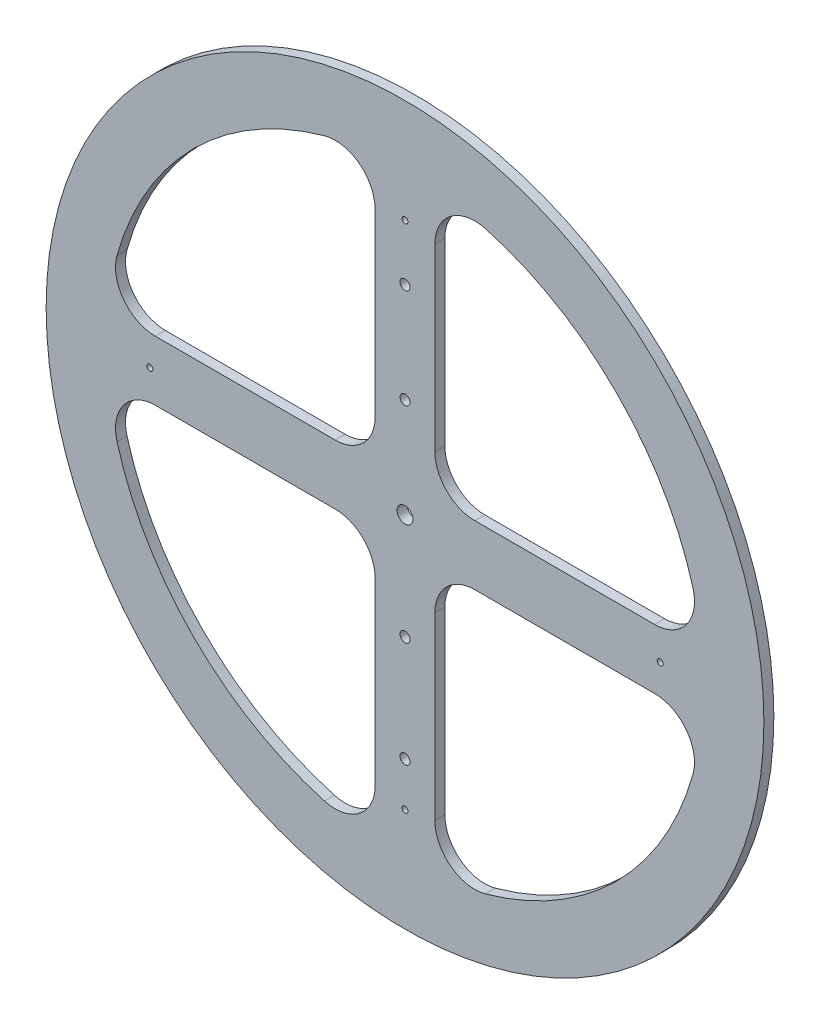
SolidWorks part; units mm, degrees
other "DetailItem2"
ref_plane "Front Plane" through (0, 0, 0) normal (0, 0, 1) x (1, 0, 0)
ref_plane "Top Plane" through (0, 0, 0) normal (0, 1, 0) x (1, 0, 0)
ref_plane "Right Plane" through (0, 0, 0) normal (1, 0, 0) x (0, 0, -1)
sketch "Sketch1" plane through (0, 0, 0) normal (0, 0, 1) x (1, 0, 0)
  line L0 (-150, 0) -> (150, 0) construction
  line L1 (0, 150) -> (0, -150) construction
  line L2 (-15, 125.1998) -> (-15, 35)
  line L3 (15, 125.1998) -> (15, 35)
  line L4 (-15, 150) -> (-15, -150) construction
  line L5 (0, 0) -> (228.291, 228.291) construction
  line L6 (125.1998, 15) -> (35, 15)
  line L7 (125.1998, -15) -> (35, -15)
  line L8 (15, -35) -> (15, -125.1998)
  line L9 (-15, -35) -> (-15, -125.1998)
  line L10 (-35, -15) -> (-125.1998, -15)
  line L11 (-35, 15) -> (-125.1998, 15)
  circle A0 centre (0, 0) radius 180
  arc A1 (144.4614, 40.3846) -> (40.3846, 144.4614) centre (0, 0) ccw
  arc A2 (-40.3846, 144.4614) -> (-144.4614, 40.3846) centre (0, 0) ccw
  arc A3 (40.3846, -144.4614) -> (144.4614, -40.3846) centre (0, 0) ccw
  arc A4 (-144.4614, -40.3846) -> (-40.3846, -144.4614) centre (0, 0) ccw
  arc A5 (-125.1998, -15) -> (-144.4614, -40.3846) centre (-125.1998, -35) ccw
  arc A6 (-15, -125.1998) -> (-40.3846, -144.4614) centre (-35, -125.1998) cw
  arc A7 (40.3846, -144.4614) -> (15, -125.1998) centre (35, -125.1998) cw
  arc A8 (144.4614, -40.3846) -> (125.1998, -15) centre (125.1998, -35) ccw
  arc A9 (125.1998, 15) -> (144.4614, 40.3846) centre (125.1998, 35) ccw
  arc A10 (40.3846, 144.4614) -> (15, 125.1998) centre (35, 125.1998) ccw
  arc A11 (-15, 125.1998) -> (-40.3846, 144.4614) centre (-35, 125.1998) ccw
  arc A12 (-144.4614, 40.3846) -> (-125.1998, 15) centre (-125.1998, 35) ccw
  arc A13 (-35, -15) -> (-15, -35) centre (-35, -35) cw
  arc A14 (15, -35) -> (35, -15) centre (35, -35) cw
  arc A15 (35, 15) -> (15, 35) centre (35, 35) cw
  arc A16 (-15, 35) -> (-35, 15) centre (-35, 35) cw
  point P24 (-149.2481, -15)
  point P27 (-15, -149.2481)
  point P30 (15, -149.2481)
  point P33 (149.2481, -15)
  point P36 (149.2481, 15)
  point P39 (15, 149.2481)
  point P42 (-15, 149.2481)
  point P45 (-149.2481, 15)
  point P48 (-15, -15)
  point P53 (15, 15)
  dimension "D1" = 360
  dimension "D2" = 300
  dimension "D5" = 20
  dimension "D4" = 45
  dimension "D3" = 15
extrude "Boss-Extrude1" add sketch "Sketch1" along normal blind 5
sketch "Sketch2" plane through (0, 0, 5) normal (0, 0, 1) x (1, 0, 0)
  circle A0 centre (0, 0) radius 4
  dimension "D1" = 8
extrude "Cut-Extrude1" cut sketch "Sketch2" against normal through all
sketch "Sketch3" plane through (0, 0, 5) normal (0, 0, 1) x (1, 0, 0)
  line L0 (0, 0) -> (0, 149.8543) construction
  line L1 (0, 0) -> (0, -168.5485) construction
  circle A0 centre (0, 50) radius 2.5
  circle A1 centre (0, 100) radius 2.5
  circle A2 centre (0, -53) radius 2.5
  circle A3 centre (0, -106) radius 2.5
  circle A4 centre (0, 0) radius 4 construction
  dimension "D1" = 5
  dimension "D3" = 50
  dimension "D4" = 53
  dimension "D5" = 53
  dimension "D2" = 50
extrude "Cut-Extrude2" cut sketch "Sketch3" against normal through all
sketch "Sketch4" plane through (0, 0, 5) normal (0, 0, 1) x (1, 0, 0)
  circle A0 centre (0, 0) radius 128 construction
  circle A1 centre (0, 128) radius 1.5
  circle A2 centre (128, 0) radius 1.5
  circle A3 centre (0, -128) radius 1.5
  circle A4 centre (-128, 0) radius 1.5
  dimension "D1" = 256
  dimension "D2" = 3
extrude "Cut-Extrude3" cut sketch "Sketch4" against normal through all
